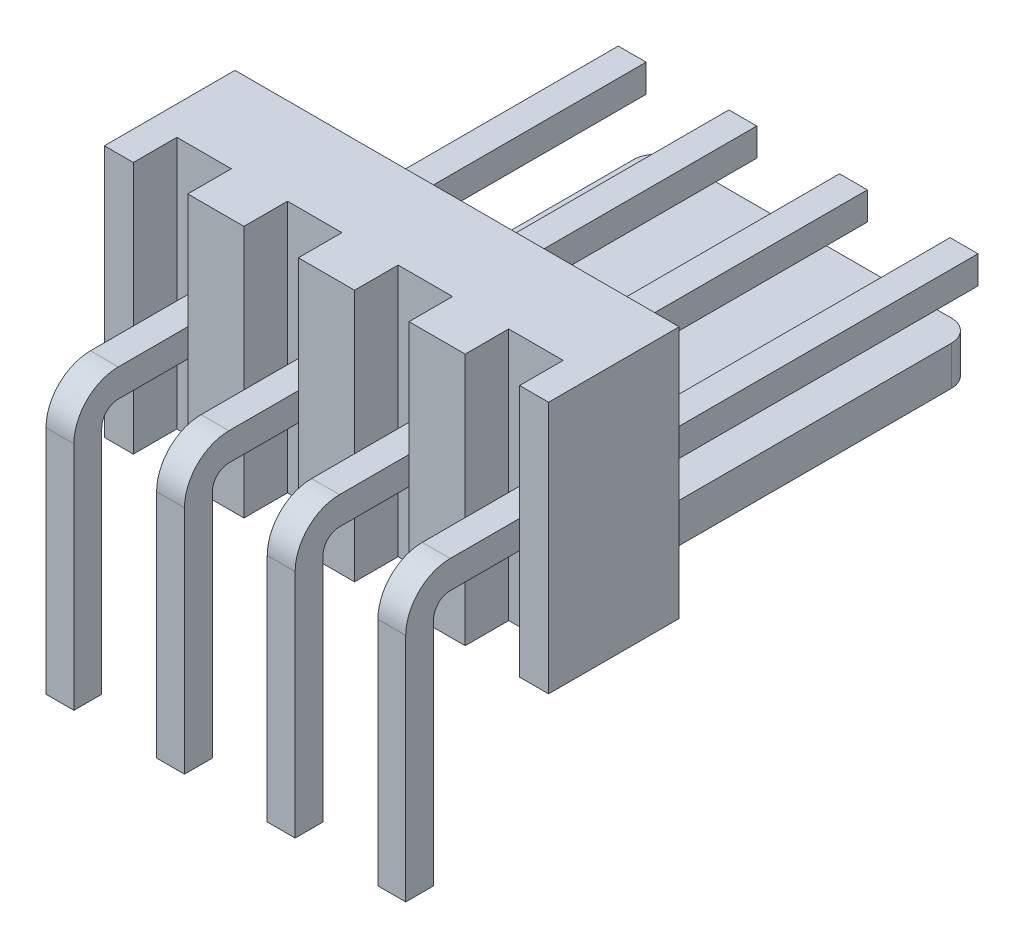
SolidWorks part; units mm, degrees
ref_plane "Piano frontale" through (0, 0, 0) normal (0, 0, 1) x (1, 0, 0)
ref_plane "Piano superiore" through (0, 0, 0) normal (0, 1, 0) x (1, 0, 0)
ref_plane "Piano destro" through (0, 0, 0) normal (1, 0, 0) x (0, 0, -1)
sketch "Schizzo1" plane through (0, 0, 0) normal (0, 0, 1) x (1, 0, 0)
  line L1 (-5.1, -2.9) -> (5.1, -2.9)
  line L2 (-5.1, -2.9) -> (-5.1, 2.9)
  line L3 (-5.1, 2.9) -> (5.1, 2.9)
  line L4 (5.1, -2.9) -> (5.1, 2.9)
  line L5 (-5.1, -2.9) -> (5.1, 2.9) construction
  line L6 (-5.1, 2.9) -> (5.1, -2.9) construction
  point P0 (0, 0)
  dimension "D1" = 10.2
  dimension "D2" = 5.8
extrude "Estrusione-Estrusione1" add sketch "Schizzo1" along normal blind 3
sketch "Schizzo2" plane through (0, 2.9, 0) normal (0, 1, 0) x (1, 0, 0)
  line L0 (-4.435, -3) -> (-4.435, -2)
  line L1 (5.1, -3) -> (-5.1, -3) construction
  line L2 (-4.435, -2) -> (-3.185, -2)
  line L3 (-3.185, -2) -> (-3.185, -3)
  line L4 (-3.185, -3) -> (-1.895, -3)
  line L5 (-1.895, -3) -> (-1.895, -2)
  line L6 (-1.895, -2) -> (-0.645, -2)
  line L7 (-0.645, -2) -> (-0.645, -3)
  line L8 (-0.645, -3) -> (0.645, -3)
  line L9 (0.645, -3) -> (0.645, -2)
  line L10 (0.645, -2) -> (1.895, -2)
  line L11 (1.895, -2) -> (1.895, -3)
  line L12 (1.895, -3) -> (3.185, -3)
  line L13 (3.185, -3) -> (3.185, -2)
  line L14 (3.185, -2) -> (4.435, -2)
  line L15 (4.435, -2) -> (4.435, -3)
  line L16 (4.435, -3) -> (4.435, -3.5613)
  line L17 (4.435, -3.5613) -> (-4.435, -3.5613)
  line L18 (-4.435, -3.5613) -> (-4.435, -3)
  line L19 (-5.1, -3) -> (-5.1, 0) construction
  point P20 (1.27, -2)
  point P21 (3.81, -2)
  point P22 (-3.81, -2)
  point P23 (-1.27, -2)
  dimension "D1" = 1.25
  dimension "D2" = 1
  dimension "D3" = 2.54
  dimension "D4" = 2.54
  dimension "D5" = 2.54
  dimension "D6" = 0.665
extrude "Taglio-Estrusione1" cut sketch "Schizzo2" against normal through all
sketch "Schizzo3" plane through (0, 0, 0) normal (0, 0, -1) x (-1, 0, 0)
  line L0 (5.1, -2.9) -> (-5.1, -2.9) construction
  line L1 (-3.65, -2.9) -> (3.65, -2.9)
  line L2 (-3.65, -2.9) -> (-3.65, -2)
  line L3 (-3.65, -2) -> (3.65, -2)
  line L4 (3.65, -2.9) -> (3.65, -2)
  point P6 (0, -2)
  dimension "D1" = 7.3
  dimension "D2" = 0.9
extrude "Estrusione-Estrusione2" add sketch "Schizzo3" along normal blind 8.2
fillet "Raccordo1" radius 0.5 2 edges at (-3.65, -2.45, -8.2) (3.65, -2.45, -8.2)
ref_plane "Piano1" through (1.28, 0, 0) normal (1, 0, 0) x (0, 0, -1)
sketch "Schizzo5" plane through (1.28, 0, 0) normal (1, 0, 0) x (0, 0, -1)
  line L0 (-4.3, -0.357) -> (8, -0.357) construction
  line L1 (7.7, -2.9) -> (0, -2.9) construction
  line L2 (0, -2.9) -> (0, 2.9) construction
  line L3 (-3, -2.9) -> (-3, 2.9) construction
  line L4 (-5, -1.057) -> (-5, -6.357) construction
  line L5 (-4.3, -0.037) -> (8, -0.037)
  line L6 (-5.32, -1.057) -> (-5.32, -6.357)
  line L7 (-4.3, -0.677) -> (8, -0.677)
  line L8 (-4.68, -1.057) -> (-4.68, -6.357)
  line L9 (8, -0.037) -> (8, -0.677)
  line L10 (-5.32, -6.357) -> (-4.68, -6.357)
  arc A0 (-5, -1.057) -> (-4.3, -0.357) centre (-4.3, -1.057) cw construction
  arc A1 (-5.32, -1.057) -> (-4.3, -0.037) centre (-4.3, -1.057) cw
  arc A2 (-4.68, -1.057) -> (-4.3, -0.677) centre (-4.3, -1.057) cw
  point P11 (-5, -0.357)
  dimension "D5" = 0.7
  dimension "D1" = 2.543
  dimension "D2" = 8
  dimension "D3" = 2
  dimension "D4" = 6
  dimension "D6" = 0.32
  dimension "D7" = 0.32
extrude "Estrusione-Estrusione3" add sketch "Schizzo5" along normal mid plane 0.64
pattern_linear "Ripetizione a L1" count 3 spacing 2.54 along (-1, 0, 0) count 2 spacing 2.54 along (1, 0, 0) of "Estrusione-Estrusione3"
chamfer "Smusso1" distance 0.18 angle 45 16 edges at (-3.48, -0.357, -8) (-3.8, -0.037, -8) (-4.12, -0.357, -8) (-3.8, -0.677, -8) (-0.94, -0.357, -8) (-1.26, -0.037, -8) (-1.26, -0.677, -8) (-1.58, -0.357, -8) (1.28, -0.037, -8) (1.6, -0.357, -8) (1.28, -0.677, -8) (0.96, -0.357, -8) (3.82, -0.037, -8) (3.5, -0.357, -8) (3.82, -0.677, -8) (4.14, -0.357, -8)
